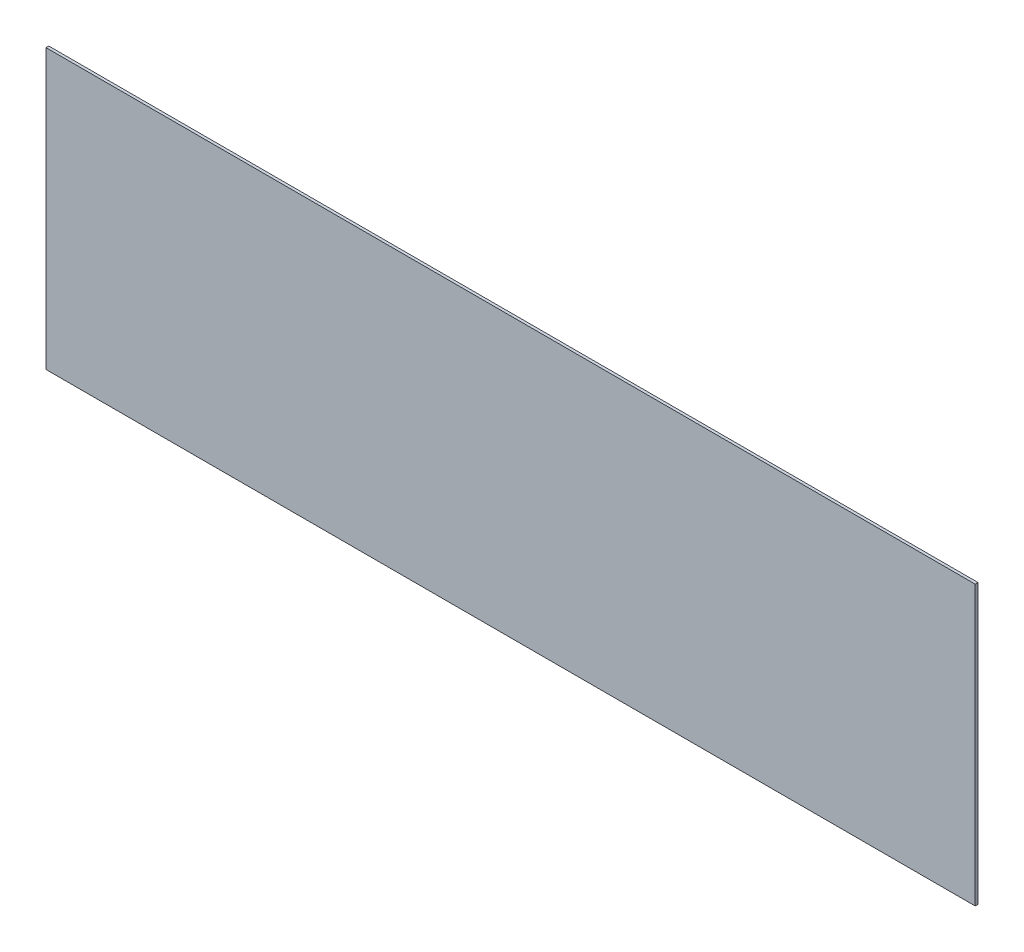
SolidWorks part; units mm, degrees
material "Balsa"
ref_plane "Front Plane" through (0, 0, 0) normal (0, 0, 1) x (1, 0, 0)
ref_plane "Top Plane" through (0, 0, 0) normal (0, 1, 0) x (1, 0, 0)
ref_plane "Right Plane" through (0, 0, 0) normal (1, 0, 0) x (0, 0, -1)
sketch "Sketch1" plane through (0, 0, 0) normal (0, 0, 1) x (1, 0, 0)
  line L1 (0, 0) -> (500, 0)
  line L2 (0, 0) -> (0, -150)
  line L3 (0, -150) -> (500, -150)
  line L4 (500, 0) -> (500, -150)
  dimension "D1" = 150
  dimension "D2" = 500
extrude "Boss-Extrude1" add sketch "Sketch1" along normal blind 1.5
